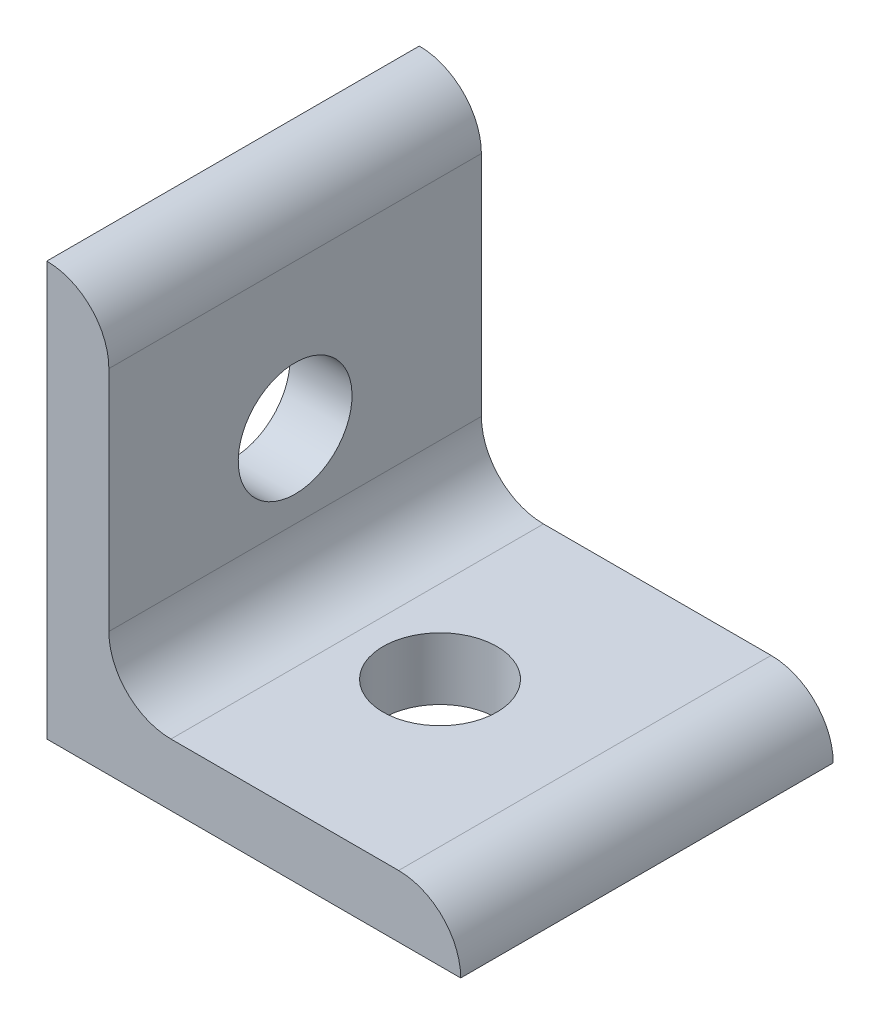
SolidWorks part; units mm, degrees
ref_plane "Front Plane" through (0, 0, 0) normal (0, 0, 1) x (1, 0, 0)
ref_plane "Top Plane" through (0, 0, 0) normal (0, 1, 0) x (1, 0, 0)
ref_plane "Right Plane" through (0, 0, 0) normal (1, 0, 0) x (0, 0, -1)
sketch "Sketch1" plane through (0, 0, 0) normal (0, 0, 1) x (1, 0, 0)
  line L0 (0, 0) -> (0, 20)
  line L1 (3, 17) -> (3, 20) construction
  line L2 (3, 17) -> (3, 6)
  line L3 (6, 3) -> (17, 3)
  line L4 (3, 20) -> (0, 20) construction
  line L5 (20, 0) -> (0, 0)
  line L6 (17, 3) -> (20, 3) construction
  line L7 (20, 3) -> (20, 0) construction
  arc A0 (3, 17) -> (0, 20) centre (0, 17) ccw
  arc A1 (20, 0) -> (17, 3) centre (17, 0) ccw
  arc A2 (3, 6) -> (6, 3) centre (6, 6) ccw
  point P10 (3, 18.5)
  dimension "E" = 3
  dimension "D" = 3
  dimension "C" = 20
  dimension "B" = 20
extrude "Boss-Extrude1" add sketch "Sketch1" along normal mid plane 18
sketch "Sketch2" plane through (0, 0, 0) normal (0, 1, 0) x (1, 0, 0)
  line L0 (0, 0) -> (10, 0) construction
  circle A0 centre (10, 0) radius 2.75
extrude "Cut-Extrude1" cut sketch "Sketch2" along normal through all
sketch "Sketch3" plane through (0, 0, 0) normal (1, 0, 0) x (0, 0, -1)
  line L0 (0, 0) -> (0, 10) construction
  circle A0 centre (0, 10) radius 2.75
  dimension "D1" = 10
extrude "Cut-Extrude2" cut sketch "Sketch3" along normal through all
equation "\"E@Sketch3\" = \"E@Sketch2\""
equation "\"D1@Sketch3\" = \"D1@Sketch2\""
